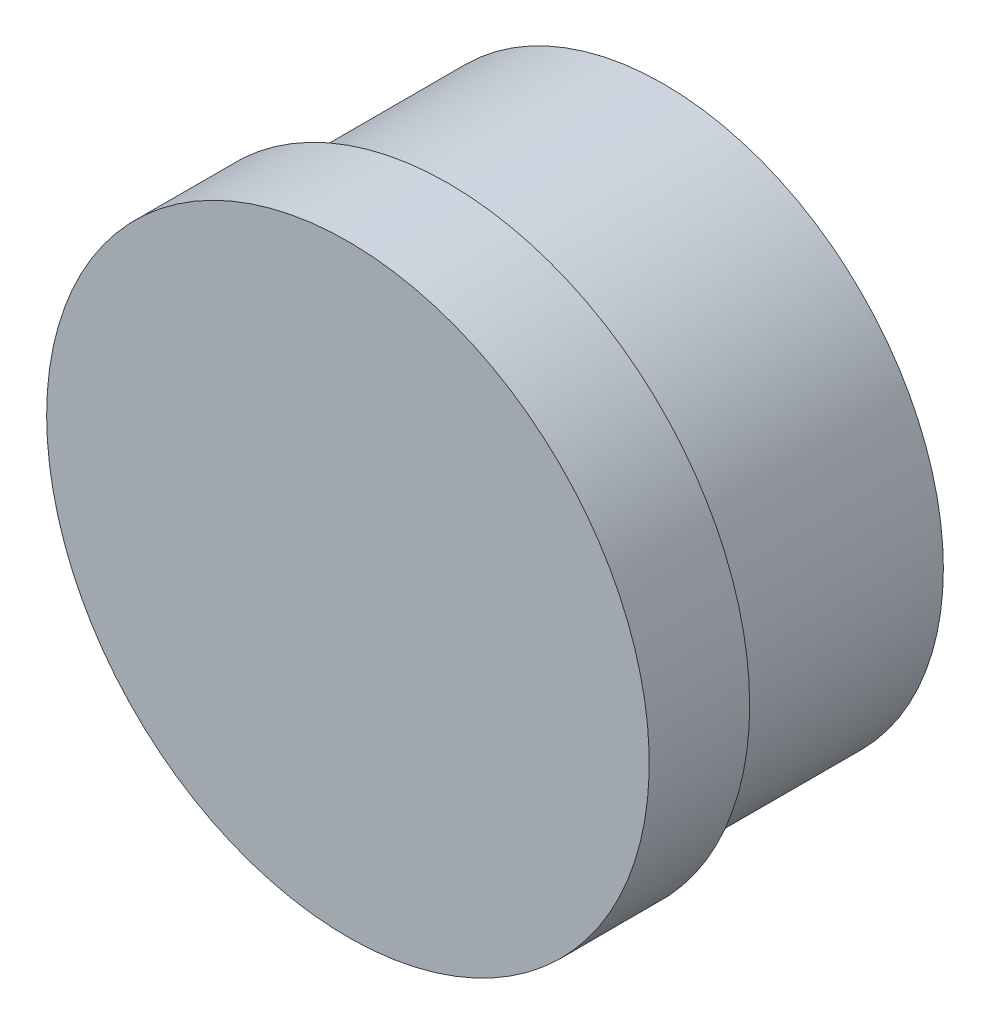
SolidWorks part; units mm, degrees
ref_plane "Front Plane" through (0, 0, 0) normal (0, 0, 1) x (1, 0, 0)
ref_plane "Top Plane" through (0, 0, 0) normal (0, 1, 0) x (1, 0, 0)
ref_plane "Right Plane" through (0, 0, 0) normal (1, 0, 0) x (0, 0, -1)
sketch "Sketch1" plane through (0, 0, 0) normal (0, 0, 1) x (1, 0, 0)
  circle A0 centre (0, 0) radius 19.5
  dimension "D1" = 39
extrude "Boss-Extrude1" add sketch "Sketch1" along normal blind 15
sketch "Sketch2" plane through (0, 0, 15) normal (0, 0, 1) x (1, 0, 0)
  circle A0 centre (0, 0) radius 21
  dimension "D1" = 42
extrude "Boss-Extrude2" add sketch "Sketch2" along normal blind 2
sketch "Sketch3" plane through (0, 0, 17) normal (0, 0, 1) x (1, 0, 0)
  circle A0 centre (0, 0) radius 50
  dimension "D1" = 100
extrude "Boss-Extrude3" add sketch "Sketch3" along normal blind 5
sketch "Sketch4" plane through (0, 0, 17) normal (0, 0, -1) x (-1, 0, 0)
  line L0 (0, 50) -> (0, 21) construction
  line L1 (-21, 0) -> (-50, 0) construction
  line L2 (0, 0) -> (-10.5, 18.1865) construction
  line L3 (0, 0) -> (10.5, 18.1865) construction
  line L4 (-10.5, 18.1865) -> (-21.25, 36.8061)
  line L5 (10.5, 18.1865) -> (21.4846, 36.6696)
  line L6 (18.1865, -10.5) -> (36.6696, -21.4846)
  line L7 (18.1865, 10.5) -> (36.8061, 21.25)
  line L10 (-18.1865, 10.5) -> (-36.6696, 21.4846)
  line L11 (-18.1865, -10.5) -> (-36.8061, -21.25)
  line L12 (10.5, -18.1865) -> (21.25, -36.8061) [skipped]
  line L13 (-10.5, -18.1865) -> (-21.4846, -36.6696) [skipped]
  arc A0 (-21.25, 36.8061) -> (21.4846, 36.6696) centre (0, 0) cw
  arc A1 (-10.5, 18.1865) -> (10.5, 18.1865) centre (0, 0) cw
  arc A2 (36.8061, 21.25) -> (36.6696, -21.4846) centre (0, 0) cw
  circle A3 centre (0, 0) radius 50 construction
  circle A4 centre (0, 0) radius 21 construction
  arc A5 (18.1865, 10.5) -> (18.1865, -10.5) centre (0, 0) cw
  circle A6 centre (0, 0) radius 21 construction
  arc A9 (-36.8061, -21.25) -> (-36.6696, 21.4846) centre (0, 0) cw
  arc A10 (-18.1865, -10.5) -> (-18.1865, 10.5) centre (0, 0) cw
  arc A11 (21.25, -36.8061) -> (-21.4846, -36.6696) centre (0, 0) cw [skipped]
  arc A12 (10.5, -18.1865) -> (-10.5, -18.1865) centre (0, 0) cw [skipped]
  circle M8 centre (0, 0) radius 21
  dimension "D2" = 42.5
  dimension "D1" = 30
  dimension "D3" = 4
extrude "Cut-Extrude2" cut sketch "Sketch4" against normal blind 5 contours A9 L11 L10 M8 | A0 L4 L5 M8 | A2 L7 L6 M8
sketch "Sketch5" plane through (0, 0, 22) normal (0, 0, 1) x (1, 0, 0)
  line L0 (-15, -47.697) -> (-15, -27.697)
  line L1 (-15, -27.697) -> (15, -27.697)
  line L2 (15, -27.697) -> (15, -47.697)
  circle A0 centre (0, 0) radius 50 construction
  arc A1 (-15, -47.697) -> (15, -47.697) centre (0, 0) ccw
  circle M1 centre (0, 0) radius 50
  dimension "D1" = 15
  dimension "D2" = 15
  dimension "D3" = 20
extrude "Cut-Extrude3" cut sketch "Sketch5" against normal blind 2.5 contours L2 L1 L0 M1
sketch "Sketch8" plane through (0, 0, 19.5) normal (0, 0, 1) x (1, 0, 0)
  line L0 (-15, -27.697) -> (15, -27.697) construction
  line L1 (-15, -27.697) -> (15, -27.697) construction
  circle A0 centre (-7.5, -37.697) radius 2.5
  circle A1 centre (7.5, -37.697) radius 2.5
  dimension "D1" = 5
  dimension "D2" = 5
  dimension "D3" = 7.5
  dimension "D4" = 7.5
  dimension "D5" = 10
  dimension "D6" = 10
extrude "Cut-Extrude4" cut sketch "Sketch8" against normal through all
sketch "Sketch9" plane through (0, 0, 22) normal (0, 0, 1) x (1, 0, 0)
  line L0 (-36.8061, 21.25) -> (-43.3013, 25)
  line L1 (-36.6696, -21.4846) -> (-43.117, -25.3164)
  line L2 (-21.4846, 36.6696) -> (-25.3164, 43.117)
  line L3 (21.25, 36.8061) -> (25, 43.3013)
  line L4 (36.6696, 21.4846) -> (43.117, 25.3164)
  line L5 (36.8061, -21.25) -> (43.3013, -25)
  line L9 (21.4846, -36.6696) -> (25.3164, -43.117) [skipped]
  line L10 (-21.25, -36.8061) -> (-25, -43.3013) [skipped]
  arc A0 (15, -47.697) -> (-15, -47.697) centre (0, 0) ccw construction
  arc A1 (-43.117, -25.3164) -> (-43.3013, 25) centre (0, 0) cw
  arc A2 (-36.8061, 21.25) -> (-36.6696, -21.4846) centre (0, 0) ccw
  arc A3 (21.25, 36.8061) -> (-21.4846, 36.6696) centre (0, 0) ccw
  arc A4 (-25.3164, 43.117) -> (25, 43.3013) centre (0, 0) cw
  arc A5 (36.8061, -21.25) -> (36.6696, 21.4846) centre (0, 0) ccw
  arc A6 (43.117, 25.3164) -> (43.3013, -25) centre (0, 0) cw
  arc A10 (25.3164, -43.117) -> (-25, -43.3013) centre (0, 0) cw [skipped]
  arc A11 (-21.25, -36.8061) -> (21.4846, -36.6696) centre (0, 0) ccw [skipped]
  dimension "D1" = 4
extrude "Boss-Extrude4" add sketch "Sketch9" along normal blind 5
fillet "Fillet1" radius 1 12 edges at (-39.8933, -23.4005, 27) (-49.9997, -0.1831, 27) (-40.0537, 23.125, 27) (-42.4998, -0.1357, 27) (40.0537, -23.125, 27) (42.4998, 0.1357, 27) (49.9997, 0.1831, 27) (39.8933, 23.4005, 27) (23.125, 40.0537, 27) (-0.1831, 49.9997, 27) (-23.4005, 39.8933, 27) (-0.1357, 42.4998, 27)
sketch "Sketch10" plane through (0, 0, 0) normal (0, 0, -1) x (-1, 0, 0)
  circle A0 centre (0, 0) radius 21
  circle A1 centre (0, 0) radius 50
extrude "Cut-Extrude5" cut sketch "Sketch10" against normal through all
